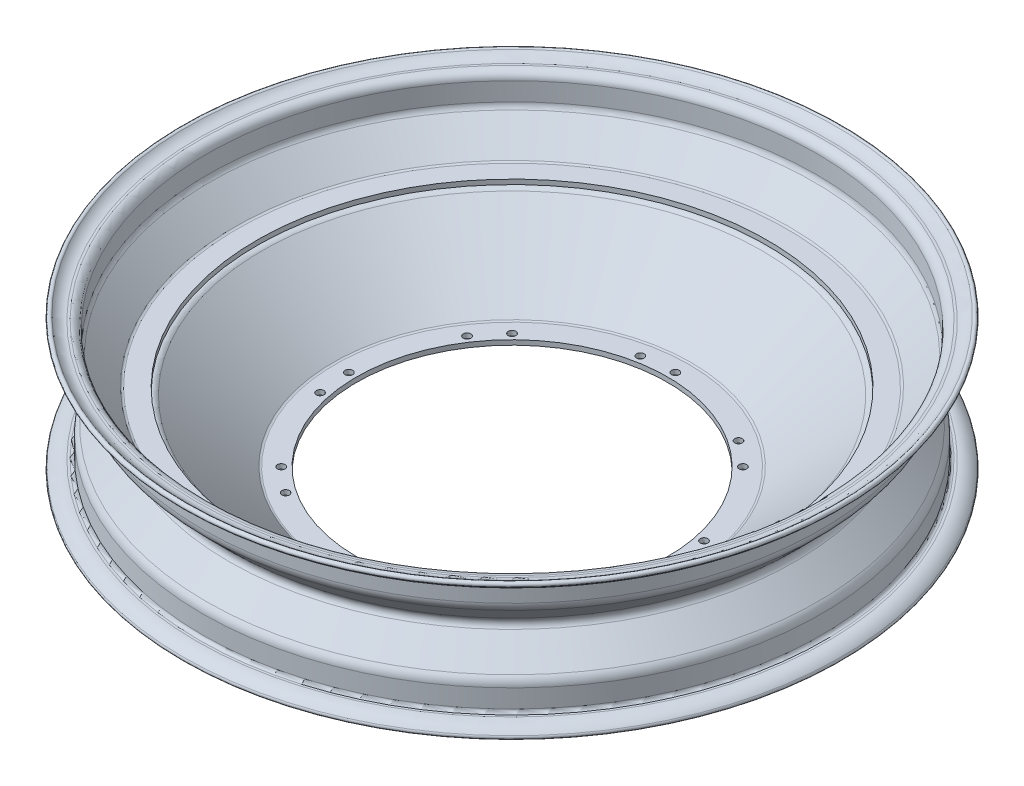
SolidWorks part; units mm, degrees
material "6061-T6 (SS)"
ref_plane "Front Plane" through (0, 0, 0) normal (0, 0, 1) x (1, 0, 0)
ref_plane "Top Plane" through (0, 0, 0) normal (0, 1, 0) x (1, 0, 0)
ref_plane "Right Plane" through (0, 0, 0) normal (1, 0, 0) x (0, 0, -1)
sketch "Sketch3" plane through (0, 0, 0) normal (0, 0, 1) x (1, 0, 0)
  line L0 (-167.2903, -3.118) -> (0, 0) construction
  line L1 (-102, -48.1245) -> (-116.0972, -48.1245)
  line L2 (-167.2903, -3.118) -> (-188.5358, -3.118) construction
  line L19 (-202.8572, -39.118) -> (-202.8572, -27.118)
  line L20 (-199.7392, -27.118) -> (-199.7392, -39.118)
  line L21 (-200.4193, -21.368) -> (-185.3526, -6.3013)
  line L22 (-181.4636, -6.8393) -> (-198.2515, -23.6091)
  line L23 (-199.7392, 20.882) -> (-199.7392, 32.882)
  line L24 (-202.8572, 32.882) -> (-202.8572, 20.882)
  line L25 (-204.8572, 38) -> (-206.3572, 38)
  line L26 (-206.3572, 34.882) -> (-204.8572, 34.882)
  line L27 (-200.4193, 15.132) -> (-185.3526, 0.0653)
  line L28 (-181.4638, 0.5856) -> (-198.2514, 17.3732)
  line L29 (-167.2903, -3.118) -> (-167.2903, 0)
  line L30 (-167.2903, 0) -> (-180.0494, 0)
  line L31 (-167.2903, -6.236) -> (-180.0494, -6.236)
  line L32 (-119.4407, -46.8814) -> (-165.9837, -6.7218)
  line L33 (-163.9468, -4.3611) -> (-117.4037, -44.5208)
  line L34 (-116.0972, -45.0065) -> (-102, -45.0065)
  line L35 (-102, -45.0065) -> (-102, -48.1245)
  line L38 (-204.8572, -44.236) -> (-206.3572, -44.236)
  line L39 (-206.3572, -41.118) -> (-204.8572, -41.118)
  line L41 (0, 240.889) -> (0, -99.5724) construction
  arc A1 (-185.3526, -6.3013) -> (-185.3526, 0.0653) centre (-188.5358, -3.118) ccw
  arc A18 (-204.8572, -41.118) -> (-202.8572, -39.118) centre (-204.8572, -39.118) ccw
  arc A19 (-204.8572, -44.236) -> (-199.7392, -39.118) centre (-204.8572, -39.118) ccw
  arc A20 (-200.4193, -21.368) -> (-202.8572, -27.118) centre (-194.8572, -27.118) ccw
  arc A21 (-198.2515, -23.6091) -> (-199.7392, -27.118) centre (-194.8572, -27.118) ccw
  arc A22 (-202.8572, 20.882) -> (-200.4193, 15.132) centre (-194.8572, 20.882) ccw
  arc A23 (-199.7392, 20.882) -> (-198.2514, 17.3732) centre (-194.8572, 20.8823) ccw
  arc A24 (-202.8572, 32.882) -> (-204.8572, 34.882) centre (-204.8572, 32.882) ccw
  arc A25 (-199.7392, 32.882) -> (-204.8572, 38) centre (-204.8572, 32.882) ccw
  arc A26 (-213.3101, 41.0829) -> (-215.6209, 38.9895) centre (-214.4655, 40.0362) ccw
  arc A27 (-213.3101, 41.0829) -> (-206.3572, 38) centre (-206.3572, 47.382) ccw
  arc A28 (-215.6209, 38.9895) -> (-206.3572, 34.882) centre (-206.3572, 47.382) ccw
  arc A29 (-181.4638, 0.5856) -> (-180.0494, 0) centre (-180.0497, 2) ccw
  arc A32 (-165.9837, -6.7218) -> (-167.2903, -6.236) centre (-167.2903, -8.236) ccw
  arc A33 (-163.9468, -4.3611) -> (-167.2903, -3.118) centre (-167.2903, -8.236) ccw
  arc A34 (-119.4407, -46.8814) -> (-116.0972, -48.1245) centre (-116.0972, -43.0065) ccw
  arc A35 (-117.4037, -44.5208) -> (-116.0972, -45.0065) centre (-116.0972, -43.0065) ccw
  arc A39 (-215.6209, -45.2255) -> (-213.3101, -47.3189) centre (-214.4655, -46.2722) ccw
  arc A40 (-206.3572, -44.236) -> (-213.3101, -47.3189) centre (-206.3572, -53.618) ccw
  arc A41 (-206.3572, -41.118) -> (-215.6209, -45.2255) centre (-206.3572, -53.618) ccw
  arc A43 (-180.0494, -6.236) -> (-181.4636, -6.8393) centre (-180.032, -8.2359) ccw
  dimension "D1" = 41.8885
  dimension "D5" = 4.5018
  dimension "D6" = 3.1178
  dimension "D2" = 76
  dimension "D3" = 3.118
  dimension "D4" = 3.118
  dimension "D7" = 179.969
revolve "Revolve2" add sketch "Sketch3" angle 360 about L41
sketch "Sketch4" plane through (0, 0, 0) normal (0, 1, 0) x (1, 0, 0)
  line L0 (0, 0) -> (0, 107) construction
  line L1 (0, 0) -> (-20.8747, 104.944) construction
  circle A0 centre (0, 107) radius 2.5
  circle A1 centre (-3884.1816, -9484.2438) radius 2.5
  circle A2 centre (-13412.7463, -13519.7463) radius 2.5
  circle A3 centre (-23003.9901, -9635.5647) radius 2.5
  circle A4 centre (-27039.4925, -107) radius 2.5
  circle A5 centre (-23155.3109, 9484.2438) radius 2.5
  circle A6 centre (-13626.7463, 13519.7463) radius 2.5
  circle A7 centre (-4035.5024, 9635.5647) radius 2.5
  circle A8 centre (-20.8747, 104.944) radius 2.5
  circle A9 centre (-3900.396, -9470.937) radius 2.5
  circle A10 centre (-13414.8022, -13498.8716) radius 2.5
  circle A11 centre (-22990.6833, -9619.3503) radius 2.5
  circle A12 centre (-27018.6178, -104.944) radius 2.5
  circle A13 centre (-23139.0965, 9470.937) radius 2.5
  circle A14 centre (-13624.6903, 13498.8716) radius 2.5
  circle A15 centre (-4048.8092, 9619.3503) radius 2.5
  circle A16 centre (75.6604, 75.6604) radius 2.5
  circle A17 centre (59.446, 88.9672) radius 2.5
  circle A18 centre (107, 0) radius 2.5
  circle A19 centre (104.944, 20.8747) radius 2.5
  circle A20 centre (75.6604, -75.6604) radius 2.5
  circle A21 centre (88.9672, -59.446) radius 2.5
  circle A22 centre (0, -107) radius 2.5
  circle A23 centre (20.8747, -104.944) radius 2.5
  circle A24 centre (-75.6604, -75.6604) radius 2.5
  circle A25 centre (-59.446, -88.9672) radius 2.5
  circle A26 centre (-107, 0) radius 2.5
  circle A27 centre (-104.944, -20.8747) radius 2.5
  circle A28 centre (-75.6604, 75.6604) radius 2.5
  circle A29 centre (-88.9672, 59.446) radius 2.5
  point P19 (-13519.7463, 0)
  point P37 (-13519.7463, 0)
  point P67 (0, 0)
  dimension "D1" = 107
  dimension "D2" = 5
  dimension "D4" = 11.25
  dimension "D5" = 8
  dimension "D3" = 8
  dimension "D6" = 8
extrude "Cut-Extrude3" cut sketch "Sketch4" against normal through all both and the other way through all
